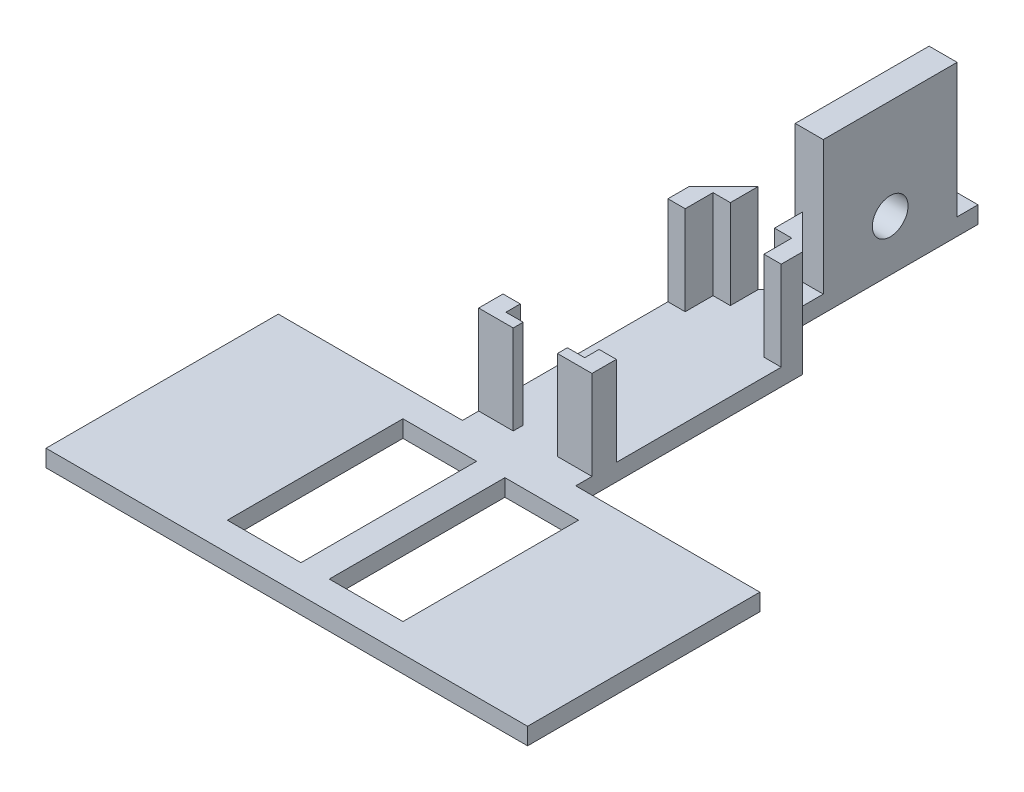
SolidWorks part; units mm, degrees
ref_plane "Front Plane" through (0, 0, 0) normal (0, 0, 1) x (1, 0, 0)
ref_plane "Top Plane" through (0, 0, 0) normal (0, 1, 0) x (1, 0, 0)
ref_plane "Right Plane" through (0, 0, 0) normal (1, 0, 0) x (0, 0, -1)
sketch "Sketch1" plane through (0, 0, 0) normal (0, 1, 0) x (1, 0, 0)
  line L0 (-53.975, 20.6803) -> (-53.975, -31.3897)
  line L1 (-3.175, 14.3303) -> (-3.175, -25.0397)
  line L3 (-19.685, 14.3303) -> (-19.685, -25.0397)
  line L4 (-19.685, -25.0397) -> (-3.175, -25.0397)
  line L8 (-19.685, 14.3303) -> (-3.175, 14.3303)
  line L9 (3.175, 14.3303) -> (19.685, 14.3303)
  line L10 (-53.975, -31.3897) -> (53.975, -31.3897)
  line L11 (-12.7, 20.6803) -> (-12.7, 71.4803)
  line L13 (12.7, 20.6803) -> (12.7, 71.4803)
  line L14 (53.975, 20.6803) -> (53.975, -31.3897)
  line L15 (-12.7, 71.4803) -> (-3.0567, 81.1236)
  line L16 (12.7, 71.4803) -> (3.2252, 80.9551)
  line L17 (19.685, -25.0397) -> (3.175, -25.0397)
  line L18 (19.685, 14.3303) -> (19.685, -25.0397)
  line L20 (3.175, 14.3303) -> (3.175, -25.0397)
  line L21 (3.2252, 80.9551) -> (3.2252, 120.3251)
  line L23 (-3.0567, 81.1236) -> (-3.0567, 120.3251)
  line L24 (-3.0567, 120.3251) -> (3.2252, 120.3251)
  line L37 (-53.975, 20.6803) -> (-12.7, 20.6803)
  line L41 (53.975, 20.6803) -> (12.7, 20.6803)
  point P16 (-12.7, 46.0803)
  point P39 (12.7, 46.0803)
  dimension "D1" = 39.37
  dimension "D2" = 3.175
  dimension "D3" = 16.51
  dimension "D4" = 6.35
  dimension "D5" = 50.8
  dimension "D6" = 6.2818
  dimension "D7" = 39.37
  dimension "D8" = 12.7
  dimension "D9" = 6.35
  dimension "D10" = 3.175
  dimension "D11" = 6.35
  dimension "D12" = 34.29
  dimension "D13" = 39.37
  dimension "D14" = 16.51
  dimension "D15" = 34.29
extrude "Boss-Extrude1" add sketch "Sketch1" along normal blind 3.81
sketch "Sketch2" plane through (0, 3.81, 0) normal (0, 1, 0) x (1, 0, 0)
  line L0 (-3.0567, 115.6401) -> (3.2252, 115.6401)
  line L1 (-3.0567, 120.3251) -> (-3.0567, 81.1236) construction
  line L2 (3.2252, 80.9551) -> (3.2252, 120.3251) construction
  line L3 (3.2252, 115.6401) -> (3.2252, 85.6401)
  line L4 (3.2252, 85.6401) -> (-3.0567, 85.6401)
  line L5 (-3.0567, 85.6401) -> (-3.0567, 115.6401)
  line L6 (3.2252, 120.3251) -> (-3.0567, 120.3251) construction
  point P10 (3.2252, 100.6401)
  dimension "D1" = 30
  dimension "D2" = 19.685
extrude "Boss-Extrude2" add sketch "Sketch2" along normal blind 30
sketch "Sketch3" plane through (3.2252, 0, 0) normal (1, 0, 0) x (0, 0, -1)
  line L0 (115.6401, 33.81) -> (115.6401, 3.81) construction
  line L1 (85.6401, 33.81) -> (85.6401, 3.81) construction
  circle A0 centre (100.6401, 11.43) radius 4
  dimension "D1" = 8
  dimension "D2" = 30
extrude "Cut-Extrude1" cut sketch "Sketch3" against normal up to next
sketch "Sketch6" plane through (0, 3.81, 0) normal (0, 1, 0) x (1, 0, 0)
  line L0 (-8.128, 24.3194) -> (-4.953, 24.3194)
  line L1 (-4.953, 24.3194) -> (-4.953, 26.5616)
  line L2 (-4.953, 26.5616) -> (-8.8291, 26.5616)
  line L3 (-8.8291, 26.5616) -> (-8.8291, 29.7795)
  line L4 (-8.8291, 29.7795) -> (-12.7, 29.7795)
  line L5 (-12.7, 29.7795) -> (-12.7, 24.3194)
  line L6 (-12.7, 24.3194) -> (-8.128, 24.3194)
  line L7 (-12.7, 71.4803) -> (-12.7, 20.6803) construction
  line L8 (0, 0) -> (0, 73.7144) construction
  line L9 (12.7, 24.3194) -> (8.128, 24.3194)
  line L10 (12.7, 29.7795) -> (12.7, 24.3194)
  line L11 (8.8291, 29.7795) -> (12.7, 29.7795)
  line L12 (8.8291, 26.5616) -> (8.8291, 29.7795)
  line L13 (4.953, 26.5616) -> (8.8291, 26.5616)
  line L14 (4.953, 24.3194) -> (4.953, 26.5616)
  line L15 (8.128, 24.3194) -> (4.953, 24.3194)
  line L16 (12.7, 46.0803) -> (-12.7, 46.0803) construction
  line L17 (12.7, 20.6803) -> (12.7, 71.4803) construction
  line L32 (-4.953, 24.3194) -> (-4.953, 86.2587) construction
  line L33 (-8.8291, 26.5616) -> (-8.8291, 87.1413) construction
  line L34 (-4.953, 79.2273) -> (-12.7, 71.4803)
  line L35 (-3.0567, 81.1236) -> (-12.7, 71.4803) construction
  line L36 (-4.953, 72.9887) -> (-8.8291, 72.9887)
  line L37 (-8.8291, 72.9887) -> (-8.8291, 66.743)
  line L38 (-8.8291, 66.743) -> (-12.7, 66.743)
  line L39 (-12.7, 66.743) -> (-12.7, 71.4803)
  line L40 (-4.953, 72.9887) -> (-4.953, 79.2273)
  line L41 (4.953, 72.9887) -> (4.953, 79.2273)
  line L42 (12.7, 66.743) -> (12.7, 71.4803)
  line L43 (8.8291, 66.743) -> (12.7, 66.743)
  line L44 (8.8291, 72.9887) -> (8.8291, 66.743)
  line L45 (4.953, 72.9887) -> (8.8291, 72.9887)
  line L46 (4.953, 79.2273) -> (12.7, 71.4803)
extrude "Boss-Extrude3" add sketch "Sketch6" along normal blind 20
